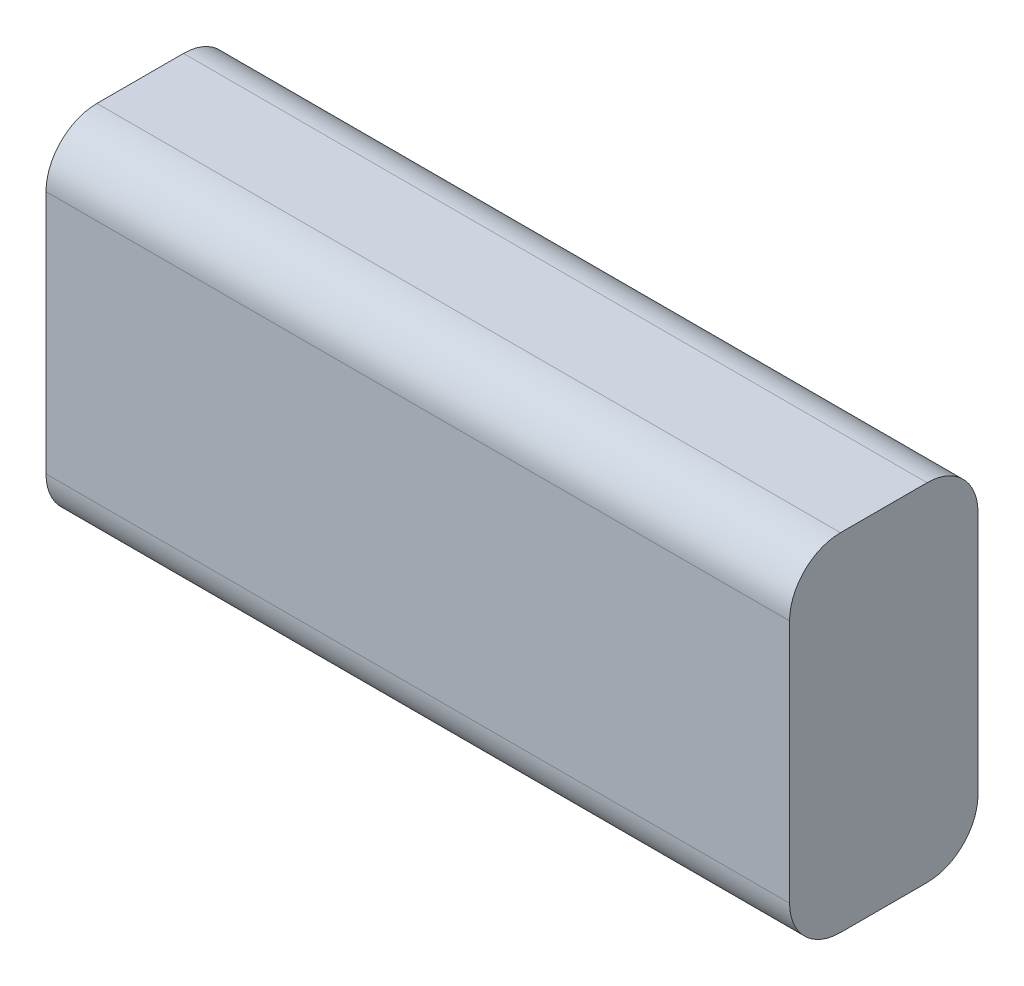
SolidWorks part; units mm, degrees
ref_plane "Front Plane" through (0, 0, 0) normal (0, 0, 1) x (1, 0, 0)
ref_plane "Top Plane" through (0, 0, 0) normal (0, 1, 0) x (1, 0, 0)
ref_plane "Right Plane" through (0, 0, 0) normal (1, 0, 0) x (0, 0, -1)
sketch "Sketch1" plane through (0, 0, 0) normal (0, 0, 1) x (1, 0, 0)
  line L1 (-27.164, 19.0688) -> (45.836, 19.0688)
  line L2 (-27.164, 19.0688) -> (-27.164, -14.9312)
  line L3 (-27.164, -14.9312) -> (45.836, -14.9312)
  line L4 (45.836, 19.0688) -> (45.836, -14.9312)
  dimension "D1" = 34
  dimension "D2" = 73
extrude "Boss-Extrude1" add sketch "Sketch1" along normal blind 18.5
fillet "Fillet1" radius 5 4 edges at (9.336, -14.9312, 0) (9.336, -14.9312, 18.5) (9.336, 19.0688, 0) (9.336, 19.0688, 18.5)
